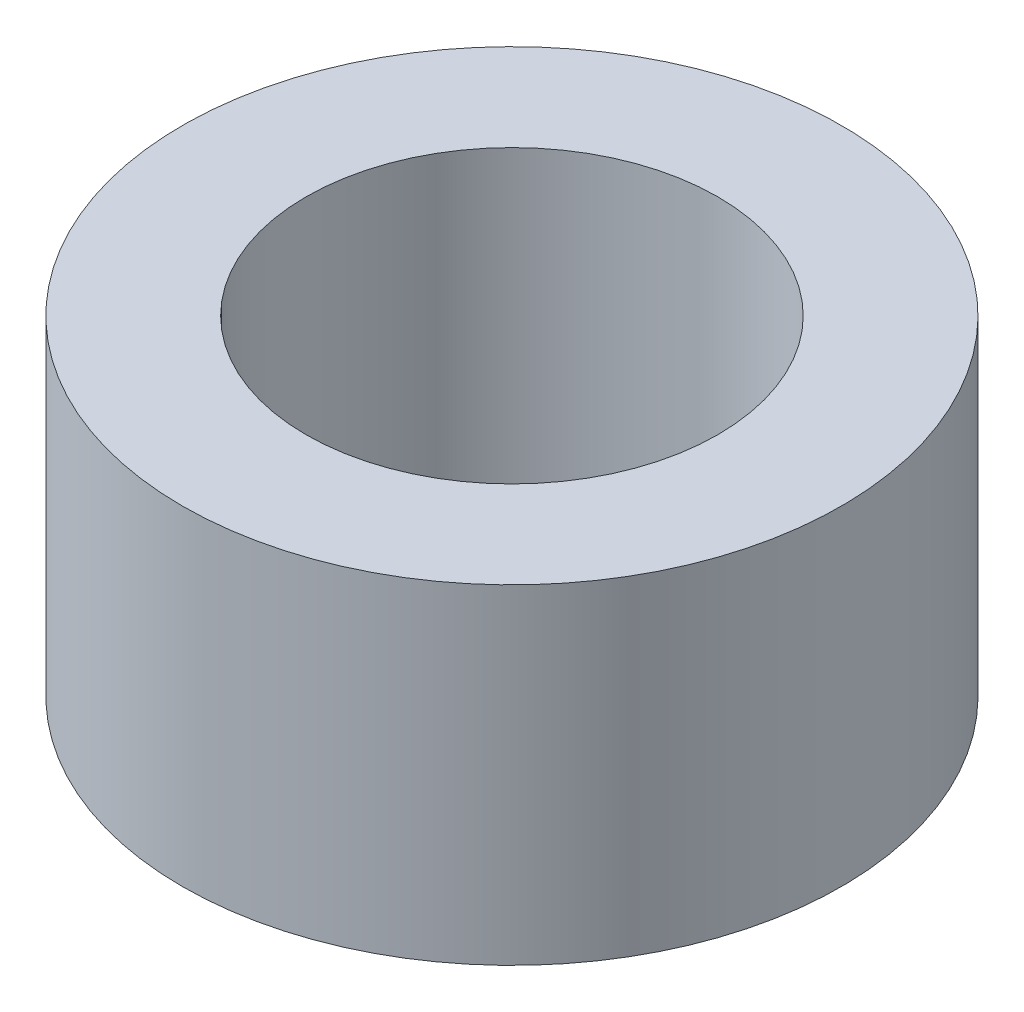
SolidWorks part; units mm, degrees
ref_plane "Front Plane" through (0, 0, 0) normal (0, 0, 1) x (1, 0, 0)
ref_plane "Top Plane" through (0, 0, 0) normal (0, 1, 0) x (1, 0, 0)
ref_plane "Right Plane" through (0, 0, 0) normal (1, 0, 0) x (0, 0, -1)
sketch "Sketch1" plane through (0, 0, 0) normal (0, 1, 0) x (1, 0, 0)
  circle A0 centre (0, 0) radius 5
  circle A1 centre (0, 0) radius 3.125
extrude "Boss-Extrude1" add sketch "Sketch1" along normal mid plane 5
